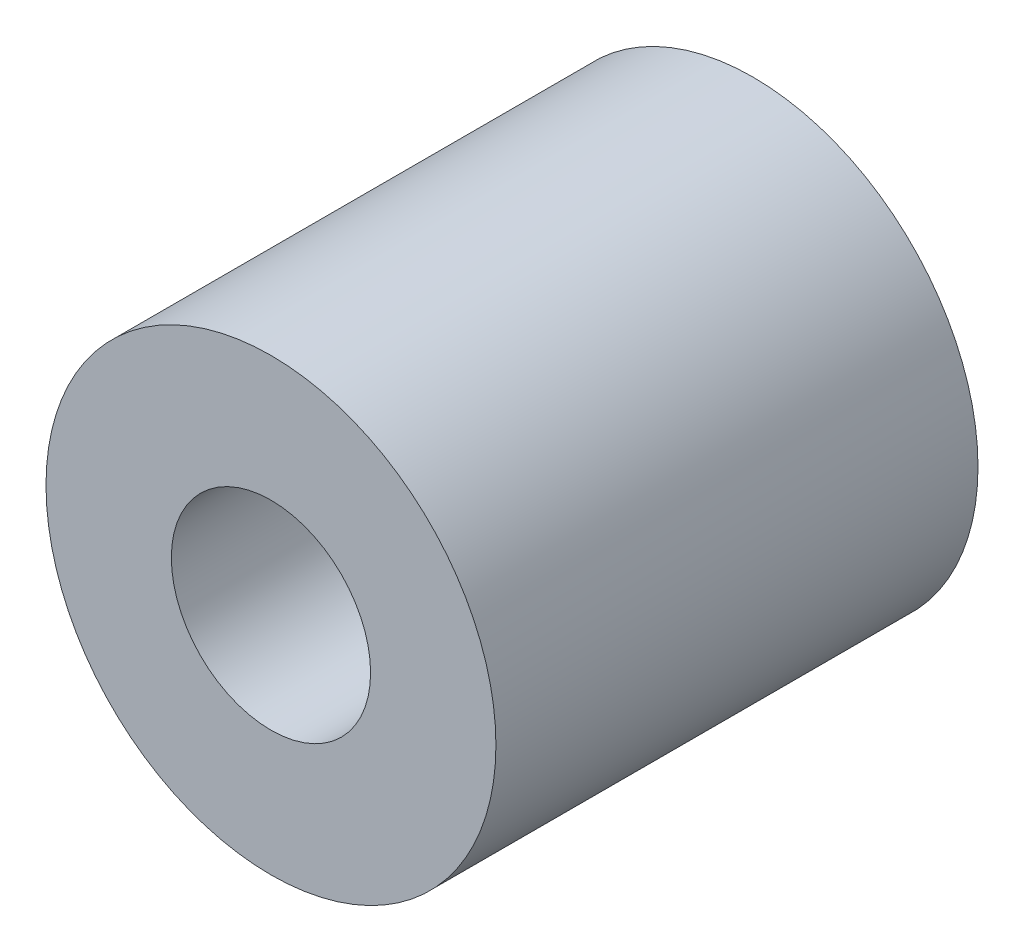
SolidWorks part; units mm, degrees
ref_plane "Front Plane" through (0, 0, 0) normal (0, 0, 1) x (1, 0, 0)
ref_plane "Top Plane" through (0, 0, 0) normal (0, 1, 0) x (1, 0, 0)
ref_plane "Right Plane" through (0, 0, 0) normal (1, 0, 0) x (0, 0, -1)
sketch "Sketch1" plane through (0, 0, 0) normal (0, 0, 1) x (1, 0, 0)
  circle A0 centre (0, 0) radius 8.89
  dimension "D1" = 17.78
extrude "Boss-Extrude2" add sketch "Sketch1" along normal blind 19.05
sketch "Sketch2" plane through (0, 0, 19.05) normal (0, 0, 1) x (1, 0, 0)
  circle A0 centre (0, 0) radius 3.937
  dimension "D1" = 7.874
extrude "Cut-Extrude1" cut sketch "Sketch2" against normal blind 19.558
sketch "Sketch3" plane through (0, 0, 0) normal (0, 0, -1) x (-1, 0, 0)
  circle A0 centre (0, 0) radius 6.223 construction
  dimension "D1" = 12.446
